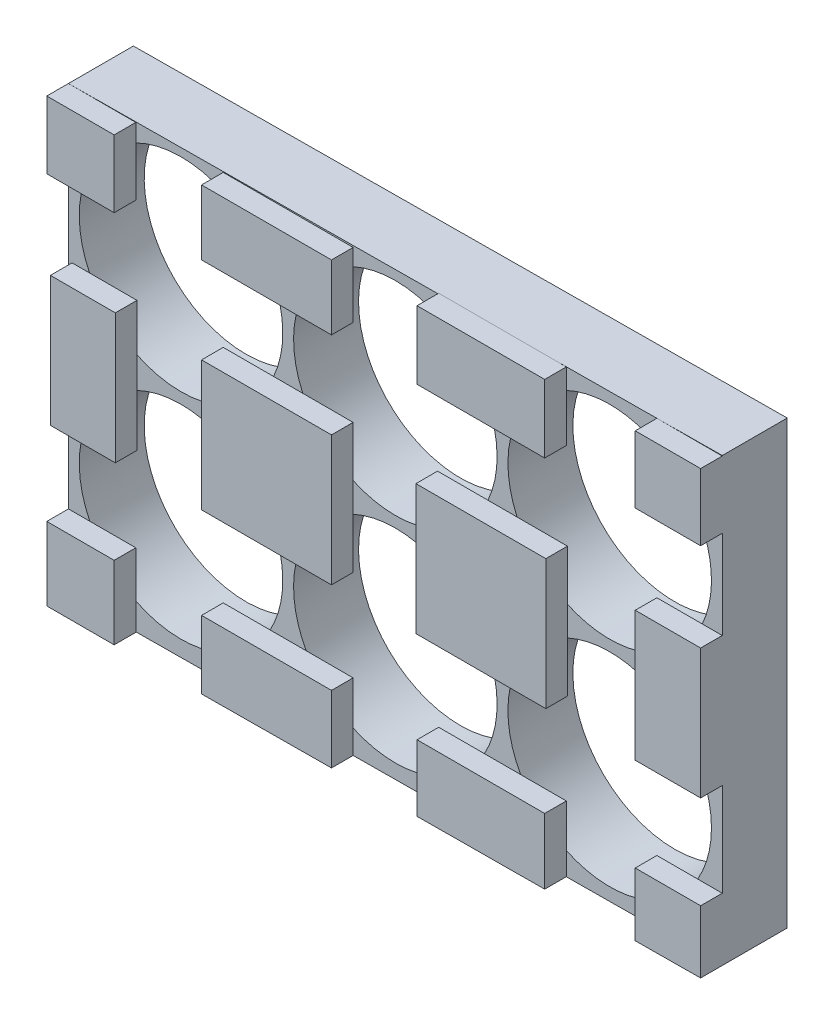
SolidWorks part; units mm, degrees
ref_plane "前视基准面" through (0, 0, 0) normal (0, 0, 1) x (1, 0, 0)
ref_plane "上视基准面" through (0, 0, 0) normal (0, 1, 0) x (1, 0, 0)
ref_plane "右视基准面" through (0, 0, 0) normal (1, 0, 0) x (0, 0, -1)
sketch "Model" plane through (0, 0, 0) normal (0, 0, 1) x (1, 0, 0)
  line L0 (1072.8622, 1168.3474) -> (1072.8622, 1127.5474)
  line L1 (1072.8622, 1168.3474) -> (1012.4638, 1167.9084)
  line L2 (1012.4638, 1167.9084) -> (1012.4638, 1127.1084)
  line L3 (1012.4638, 1127.1084) -> (1072.8622, 1127.5474)
  circle A0 centre (1022.8622, 1157.8474) radius 9.4
  circle A1 centre (1042.6622, 1157.8474) radius 9.4
  circle A2 centre (1062.4622, 1157.8474) radius 9.4
  circle A3 centre (1022.8622, 1138.0474) radius 9.4
  circle A4 centre (1042.6622, 1138.0474) radius 9.4
  circle A5 centre (1062.4622, 1138.0474) radius 9.4
  circle A6 centre (1032.7622, 1147.9474) radius 2.5
  circle A7 centre (1052.5622, 1147.9474) radius 2.5
extrude "凸台-拉伸1" add sketch "Model" along normal blind 6 contours A7 | A6 | A5 | A4 | A3 | A2 | A1 | A0 | L0 L3 L2 L1
sketch "草图2" plane through (0, 0, 6) normal (0, 0, 1) x (1, 0, 0)
  line L5 (1012.4638, 1167.9084) -> (1018.6867, 1167.9084)
  line L7 (1012.4638, 1161.6856) -> (1018.6867, 1161.6856)
  line L8 (1018.6867, 1167.9084) -> (1018.6867, 1161.6856)
  line L16 (1012.4638, 1127.1084) -> (1072.8622, 1127.5474) construction
  line L33 (1072.8622, 1168.3474) -> (1072.8622, 1127.5474) construction
  line L38 (1012.4638, 1167.9084) -> (1012.4638, 1161.6856)
  line L45 (1072.8622, 1133.3281) -> (1072.8622, 1127.5474)
  line L46 (1026.763, 1167.9445) -> (1038.763, 1167.9445)
  line L47 (1026.763, 1167.9445) -> (1026.763, 1161.9445)
  line L48 (1026.763, 1161.9445) -> (1038.763, 1161.9445)
  line L49 (1038.763, 1167.9445) -> (1038.763, 1161.9445)
  line L52 (1072.8622, 1168.3474) -> (1012.4638, 1167.9084) construction
  line L53 (1046.6672, 1168.2335) -> (1058.4572, 1168.2335)
  line L54 (1046.6672, 1168.2335) -> (1046.6672, 1161.9435)
  line L55 (1046.6672, 1161.9435) -> (1058.4572, 1161.9435)
  line L56 (1058.4572, 1168.2335) -> (1058.4572, 1161.9435)
  line L59 (1066.8225, 1168.3035) -> (1072.8622, 1168.3035)
  line L60 (1066.8225, 1168.3035) -> (1066.8225, 1162.1246)
  line L61 (1066.8225, 1162.1246) -> (1072.8622, 1162.1246)
  line L62 (1072.8622, 1168.3035) -> (1072.8622, 1162.1246)
  line L66 (1026.7622, 1153.9474) -> (1038.7622, 1153.9474)
  line L67 (1026.7622, 1153.9474) -> (1026.7622, 1141.9474)
  line L68 (1026.7622, 1141.9474) -> (1038.7622, 1141.9474)
  line L69 (1038.7622, 1153.9474) -> (1038.7622, 1141.9474)
  line L70 (1026.7622, 1153.9474) -> (1038.7622, 1141.9474) construction
  line L71 (1026.7622, 1141.9474) -> (1038.7622, 1153.9474) construction
  line L72 (1046.5622, 1153.9474) -> (1058.5622, 1153.9474)
  line L73 (1046.5622, 1153.9474) -> (1046.5622, 1141.9474)
  line L74 (1046.5622, 1141.9474) -> (1058.5622, 1141.9474)
  line L75 (1058.5622, 1153.9474) -> (1058.5622, 1141.9474)
  line L76 (1046.5622, 1153.9474) -> (1058.5622, 1141.9474) construction
  line L77 (1046.5622, 1141.9474) -> (1058.5622, 1153.9474) construction
  line L78 (1066.8225, 1153.9474) -> (1072.8622, 1153.9474)
  line L79 (1066.8225, 1153.9474) -> (1066.8225, 1141.9474)
  line L80 (1066.8225, 1141.9474) -> (1072.8622, 1141.9474)
  line L81 (1072.8622, 1153.9474) -> (1072.8622, 1141.9474)
  line L88 (1012.7964, 1153.7263) -> (1018.7964, 1153.7263)
  line L89 (1012.7964, 1153.7263) -> (1012.7964, 1141.7263)
  line L90 (1012.7964, 1141.7263) -> (1018.7964, 1141.7263)
  line L91 (1018.7964, 1153.7263) -> (1018.7964, 1141.7263)
  line L92 (1012.7964, 1153.7263) -> (1018.7964, 1141.7263) construction
  line L93 (1012.7964, 1141.7263) -> (1018.7964, 1153.7263) construction
  line L97 (1066.8225, 1133.3281) -> (1072.8622, 1127.5474) construction
  line L98 (1066.8225, 1127.5035) -> (1072.8622, 1133.3281) construction
  line L99 (1046.6672, 1133.5092) -> (1058.4572, 1127.45) construction
  line L100 (1046.6672, 1127.38) -> (1058.4572, 1133.5092) construction
  line L101 (1026.763, 1133.5081) -> (1038.763, 1127.3) construction
  line L102 (1026.763, 1127.22) -> (1038.763, 1133.5081) construction
  line L104 (1066.8225, 1133.3281) -> (1072.8622, 1133.3281)
  line L105 (1066.8225, 1127.5035) -> (1066.8225, 1133.3281)
  line L106 (1066.8225, 1127.5035) -> (1072.8622, 1127.5474)
  line L107 (1058.4572, 1127.45) -> (1058.4572, 1133.5092)
  line L108 (1046.6672, 1133.5092) -> (1058.4572, 1133.5092)
  line L109 (1046.6672, 1127.38) -> (1046.6672, 1133.5092)
  line L110 (1046.6672, 1127.38) -> (1058.4572, 1127.45)
  line L111 (1038.763, 1127.3) -> (1038.763, 1133.5081)
  line L112 (1026.763, 1133.5081) -> (1038.763, 1133.5081)
  line L113 (1026.763, 1127.22) -> (1026.763, 1133.5081)
  line L114 (1026.763, 1127.22) -> (1038.763, 1127.3)
  line L117 (1018.6867, 1127.1111) -> (1018.6867, 1133.8761)
  line L118 (1012.4638, 1133.8761) -> (1018.6867, 1133.8761)
  line L119 (1012.4638, 1127.1111) -> (1012.4638, 1133.8761)
  line L120 (1012.4638, 1127.1111) -> (1018.6867, 1127.1111)
  point P0 (0, 0)
extrude "凸台-拉伸2" add sketch "草图2" along normal blind 2
